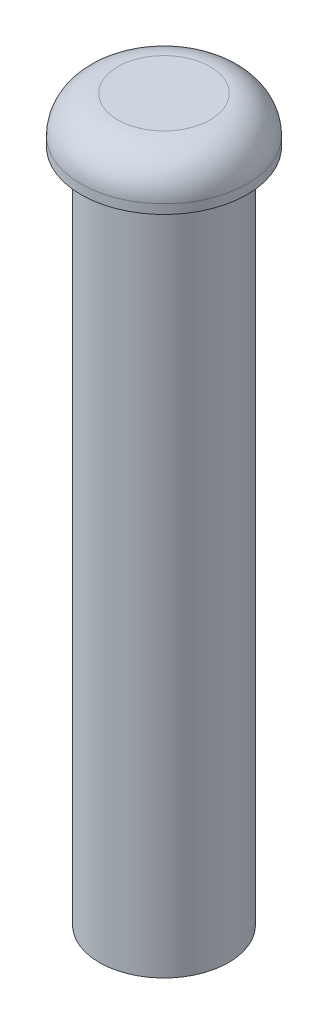
SolidWorks part; units mm, degrees
ref_plane "Front Plane" through (0, 0, 0) normal (0, 0, 1) x (1, 0, 0)
ref_plane "Top Plane" through (0, 0, 0) normal (0, 1, 0) x (1, 0, 0)
ref_plane "Right Plane" through (0, 0, 0) normal (1, 0, 0) x (0, 0, -1)
sketch "Sketch1" plane through (0, 0, 0) normal (0, 1, 0) x (1, 0, 0)
  circle A0 centre (0, 0) radius 7
  dimension "D1" = 14
extrude "Boss-Extrude1" add sketch "Sketch1" along normal blind 73
sketch "Sketch2" plane through (0, 73, 0) normal (0, 1, 0) x (1, 0, 0)
  circle A0 centre (0, 0) radius 9
  dimension "D1" = 18
extrude "Boss-Extrude2" add sketch "Sketch2" along normal blind 5
fillet "Fillet3" radius 4 1 edges at (0, 78, 9)
